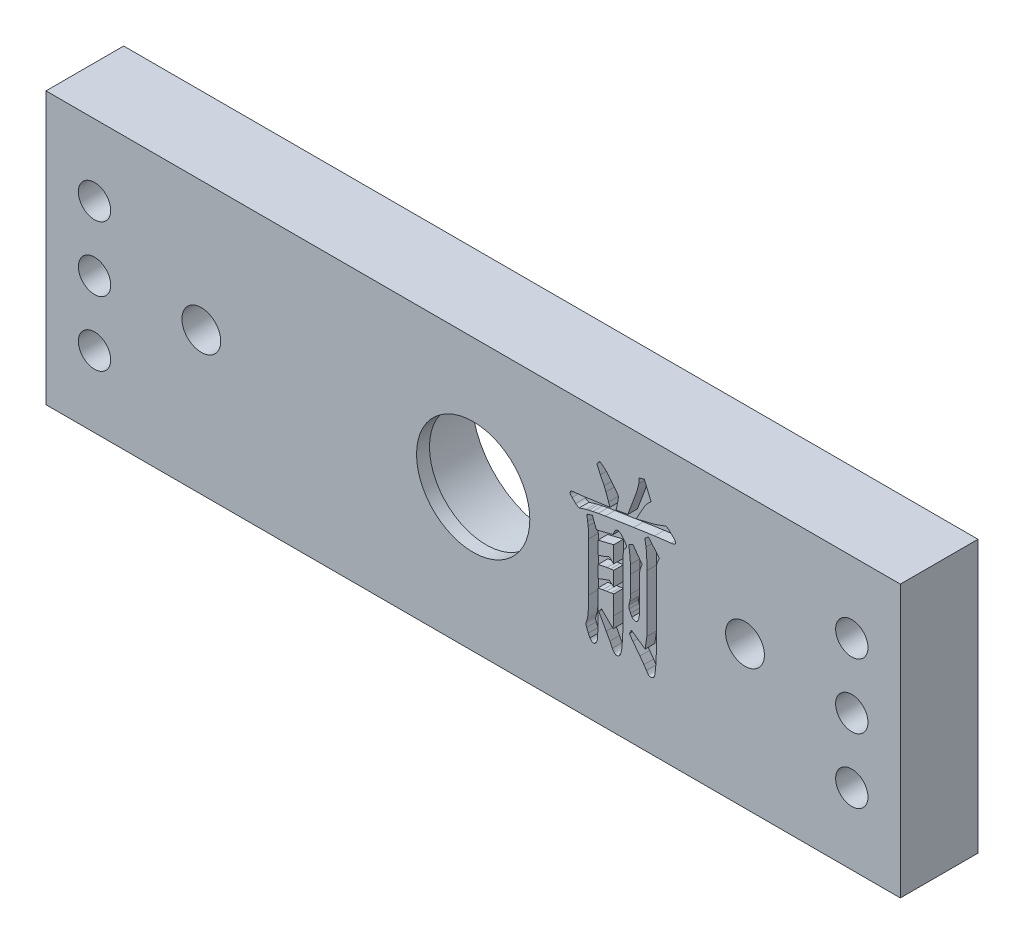
SolidWorks part; units mm, degrees
ref_plane "前视基准面" through (0, 0, 0) normal (0, 0, 1) x (1, 0, 0)
ref_plane "上视基准面" through (0, 0, 0) normal (0, 1, 0) x (1, 0, 0)
ref_plane "右视基准面" through (0, 0, 0) normal (1, 0, 0) x (0, 0, -1)
sketch "草图1" plane through (0, 0, 0) normal (0, 0, 1) x (1, 0, 0)
  line L1 (-66, 20) -> (66, 20)
  line L2 (-66, 20) -> (-66, -22)
  line L3 (-66, -22) -> (66, -22)
  line L4 (66, 20) -> (66, -22)
  dimension "D1" = 42
  dimension "D2" = 132
  dimension "D3" = 66
  dimension "D4" = 20
extrude "凸台-拉伸1" add sketch "草图1" along normal blind 12
sketch "草图2" plane through (0, 0, 0) normal (0, 0, -1) x (-1, 0, 0)
  circle A0 centre (0, 0) radius 12.25
  dimension "D1" = 24.5
extrude "切除-拉伸1" cut sketch "草图2" against normal blind 10
sketch "草图3" plane through (0, 0, 0) normal (0, 0, -1) x (-1, 0, 0)
  circle A0 centre (-42, 0) radius 4.1
  circle A1 centre (42, 0) radius 4.1
  dimension "D1" = 8.2
  dimension "D2" = 8.2
  dimension "D3" = 42
  dimension "D4" = 42
extrude "切除-拉伸2" cut sketch "草图3" against normal blind 4
sketch "草图4" plane through (0, 0, 10) normal (0, 0, -1) x (-1, 0, 0)
  circle A0 centre (0, 0) radius 8.75
  dimension "D1" = 17.5
extrude "切除-拉伸3" cut sketch "草图4" against normal blind 6
sketch "草图5" plane through (0, 0, 4) normal (0, 0, -1) x (-1, 0, 0)
  circle A0 centre (-42, 0) radius 3
  circle A1 centre (42, 0) radius 3
  dimension "D1" = 6
  dimension "D2" = 6
extrude "切除-拉伸4" cut sketch "草图5" against normal blind 8
sketch "草图6" plane through (0, 0, 12) normal (0, 0, 1) x (1, 0, 0)
  line L0 (25.1918, 8.3272) -> (27.1146, 8.7921)
  line L1 (27.1146, 8.7921) -> (27.6978, 8.9182)
  line L2 (27.6978, 8.9182) -> (28.2849, 9.0955)
  line L3 (28.2849, 9.0955) -> (28.8996, 9.328)
  line L4 (28.8996, 9.328) -> (29.1478, 9.4265)
  line L5 (29.1478, 9.4265) -> (29.8177, 9.659)
  line L6 (29.8177, 9.659) -> (30.2984, 9.328)
  line L7 (30.2984, 9.328) -> (30.8303, 8.8276)
  line L8 (30.59, 7.7716) -> (28.0209, 7.4603)
  line L9 (28.0209, 7.4603) -> (24.8095, 6.9875)
  line L10 (24.8095, 6.9875) -> (20.4003, 6.3097)
  line L11 (20.4003, 6.3097) -> (19.3207, 6.1285)
  line L12 (19.3207, 6.1285) -> (18.4696, 5.9472)
  line L13 (18.4696, 5.9472) -> (17.8707, 5.8172)
  line L14 (17.8707, 5.8172) -> (17.4924, 5.7344)
  line L15 (17.4924, 5.7344) -> (16.4009, 5.4035)
  line L16 (15.8414, 5.7226) -> (15.2976, 6.2427)
  line L17 (15.1006, 7.0544) -> (17.1299, 7.279)
  line L18 (17.1299, 7.279) -> (20.9677, 7.8267)
  line L19 (20.9677, 7.8267) -> (21.1336, 7.8433)
  line L20 (22.0543, 7.9656) -> (22.3508, 8.0119)
  line L21 (22.3508, 8.0119) -> (23.8757, 8.2484)
  line L22 (25.5858, 13.225) -> (25.6449, 14.0249)
  line L23 (25.6449, 14.0249) -> (26.4408, 14.2534)
  line L24 (26.4408, 14.2534) -> (27.489, 11.7513)
  line L25 (19.0409, 3.7879) -> (21.6061, 4.4302)
  line L26 (21.6061, 4.4302) -> (21.8661, 5.037)
  line L27 (22.9103, 5.0725) -> (23.4186, 4.4381)
  line L28 (23.6353, 3.7091) -> (23.2255, 3.1851)
  line L29 (23.1783, 2.2827) -> (23.1783, -5.9171)
  line L30 (21.5076, -10.8346) -> (21.1175, -10.0544)
  line L31 (21.1175, -10.0544) -> (20.5461, -9.0181)
  line L32 (20.5461, -9.0181) -> (19.3956, -6.9376)
  line L33 (19.3956, -6.9376) -> (19.829, -6.3938)
  line L34 (19.829, -6.3938) -> (21.6218, -8.1591)
  line L35 (21.7203, -6.3584) -> (21.7203, -3.4525)
  line L36 (21.7203, 3.126) -> (19.2892, 2.5388)
  line L37 (19.2892, 2.5388) -> (19.2892, 0.5214)
  line L38 (21.0032, 1.1755) -> (21.7203, 0.5627)
  line L39 (21.212, -0.373) -> (20.684, -0.4361)
  line L40 (20.684, -0.4361) -> (19.2892, -0.7316)
  line L41 (19.2892, -0.7316) -> (19.2892, -2.6111)
  line L42 (21.0465, -1.9571) -> (21.7203, -2.5391)
  line L43 (21.3066, -3.5332) -> (20.6131, -3.6356)
  line L44 (20.6131, -3.6356) -> (20.0221, -3.742)
  line L45 (20.0221, -3.742) -> (19.2892, -3.872)
  line L46 (19.2892, -3.872) -> (19.2852, -8.1394)
  line L47 (19.2852, -8.1394) -> (19.2576, -9.6604)
  line L48 (19.2576, -9.6604) -> (19.2025, -10.6809)
  line L49 (18.0322, -11.1892) -> (17.7918, -10.6809)
  line L50 (17.7918, -10.6809) -> (17.5357, -10.015)
  line L51 (17.8273, -5.5782) -> (17.8273, 1.9675)
  line L52 (17.7761, 3.654) -> (17.6736, 4.2489)
  line L53 (17.6736, 4.2489) -> (17.5673, 5.1473)
  line L54 (17.5673, 5.1473) -> (18.4105, 5.431)
  line L55 (18.4105, 5.431) -> (19.0409, 3.7879)
  line L56 (19.5847, 13.2092) -> (20.4437, 12.5197)
  line L57 (20.4437, 12.5197) -> (20.9441, 11.9404)
  line L58 (20.9441, 11.9404) -> (21.4169, 11.3651)
  line L59 (21.4169, 11.3651) -> (22.0001, 10.6559)
  line L60 (22.3863, 9.4108) -> (22.1735, 8.3626)
  line L61 (21.1293, 7.8543) -> (20.9205, 8.4611)
  line L62 (20.9205, 8.4611) -> (20.5028, 9.5999)
  line L63 (20.5028, 9.5999) -> (20.227, 10.2855)
  line L64 (20.227, 10.2855) -> (19.6556, 11.4597)
  line L65 (19.6556, 11.4597) -> (19.1079, 12.6852)
  line L66 (19.1079, 12.6852) -> (19.5847, 13.2092)
  line L67 (24.0412, 4.3199) -> (24.7032, 4.6233)
  line L68 (24.7032, 4.6233) -> (26.1296, 2.6413)
  line L69 (25.7119, 1.1322) -> (25.7119, -3.6435)
  line L70 (24.5337, -5.1448) -> (24.3249, -4.7507)
  line L71 (24.3249, -4.7507) -> (24.1082, -4.27)
  line L72 (24.0451, -3.7814) -> (24.183, -3.2771)
  line L73 (24.3288, -2.162) -> (24.3012, 0.4741)
  line L74 (24.3012, 0.4741) -> (24.3012, 1.7981)
  line L75 (24.4628, -6.9416) -> (26.5709, -8.4152)
  line L76 (26.8349, -6.5948) -> (26.8349, 2.2276)
  line L77 (26.7048, 5.3128) -> (26.5236, 6.3846)
  line L78 (26.5236, 6.3846) -> (27.0831, 6.8653)
  line L79 (27.0831, 6.8653) -> (28.7656, 4.8439)
  line L80 (28.2967, 2.3852) -> (28.2967, -8.1867)
  line L81 (28.21, -9.885) -> (28.1312, -10.6691)
  line L82 (26.7679, -11.1656) -> (26.3778, -10.5785)
  line L83 (26.3778, -10.5785) -> (25.771, -9.7234)
  line L84 (25.771, -9.7234) -> (24.6913, -8.3404)
  line L85 (24.6913, -8.3404) -> (24.1476, -7.5405)
  line L86 (24.1476, -7.5405) -> (24.4628, -6.9416)
  line L87 (21.7203, 0.5627) -> (21.7203, 3.126)
  line L88 (21.7203, -2.5391) -> (21.7203, -0.2932)
  line L89 (21.7203, -6.3584) -> (21.6218, -8.1591)
  line L90 (26.8349, -6.5948) -> (26.5709, -8.4152)
  spline S0 degree 3 poles (30.8303, 8.8276) (30.9744, 8.6945) (31.1391, 8.499) (31.2842, 8.2301) (31.2861, 8.0724) (31.1985, 7.9521) (30.9693, 7.8226) (30.7475, 7.7999) (30.59, 7.7716) knots 0 0 0 0 0.347386 0.457637 0.53741 0.613513 0.710465 1 1 1 1
  spline S1 degree 2 poles (16.4009, 5.4035) (16.0728, 5.4755) (15.8414, 5.7226) knots 0 0 0 1 1 1
  spline S2 degree 3 poles (15.2976, 6.2427) (15.214, 6.3213) (15.0998, 6.4262) (15.005, 6.5827) (14.956, 6.7793) (15.0657, 6.9388) (15.1006, 7.0544) knots 0 0 0 0 0.367731 0.487674 0.578039 1 1 1 1
  spline S3 degree 3 poles (23.8757, 8.2484) (24.0035, 8.5899) (24.2006, 9.0762) (24.4317, 9.705) (24.5935, 10.1078) (24.7245, 10.4742) (24.8484, 10.7943) (24.9507, 11.076) (25.0622, 11.386) (25.1843, 11.7218) (25.3016, 12.0834) (25.3954, 12.3954) (25.456, 12.6599) (25.5036, 12.8729) (25.5426, 13.0561) (25.5699, 13.1676) (25.5858, 13.225) knots 0 0 0 0 0.207633 0.298753 0.381388 0.45474 0.520301 0.576848 0.625344 0.707897 0.780266 0.841801 0.893317 0.934687 0.966079 1 1 1 1
  spline S4 degree 3 poles (27.489, 11.7513) (27.3166, 11.6039) (27.0782, 11.39) (26.8064, 11.0984) (26.6694, 10.9273) (26.563, 10.7652) (26.4556, 10.589) (26.3203, 10.3536) (26.1489, 10.0626) (25.9535, 9.7103) (25.627, 9.1276) (25.372, 8.6587) (25.1918, 8.3272) knots 0 0 0 0 0.163792 0.230902 0.287626 0.321818 0.370773 0.436645 0.517807 0.614614 0.727539 1 1 1 1
  spline S5 degree 3 poles (21.8661, 5.037) (21.9316, 5.1603) (22.0667, 5.3139) (22.311, 5.3773) (22.5853, 5.3094) (22.7721, 5.1729) (22.9103, 5.0725) knots 0 0 0 0 0.341138 0.451231 0.589089 1 1 1 1
  spline S6 degree 3 poles (23.4186, 4.4381) (23.4911, 4.3284) (23.591, 4.1866) (23.6748, 4.0045) (23.6983, 3.867) (23.6572, 3.7728) (23.6353, 3.7091) knots 0 0 0 0 0.489758 0.643143 0.741981 1 1 1 1
  spline S7 degree 3 poles (23.2255, 3.1851) (23.2035, 3.1054) (23.1864, 2.9905) (23.1819, 2.8278) (23.1741, 2.6085) (23.1812, 2.4219) (23.1783, 2.2827) knots 0 0 0 0 0.273514 0.382334 0.538971 1 1 1 1
  spline S8 degree 3 poles (23.1783, -5.9171) (23.1805, -6.0393) (23.1743, -6.2375) (23.1709, -6.5239) (23.1627, -6.7853) (23.1499, -7.0781) (23.1381, -7.4025) (23.1275, -7.7586) (23.1061, -8.2551) (23.0808, -8.8412) (23.0384, -9.4667) (22.99, -9.973) (22.9308, -10.3688) (22.8661, -10.6751) (22.8008, -10.9145) (22.7302, -11.0985) (22.6203, -11.2678) (22.4267, -11.3971) (22.2013, -11.4735) (21.986, -11.4379) (21.7293, -11.2415) (21.6053, -11.0036) (21.5076, -10.8346) knots 0 0 0 0 0.053419 0.086736 0.125234 0.16777 0.214897 0.267191 0.323523 0.432196 0.523735 0.597629 0.65457 0.698614 0.734431 0.763016 0.784521 0.821511 0.862616 0.885373 0.913888 1 1 1 1
  spline S10 degree 3 poles (19.2892, 0.5214) (19.6067, 0.617) (20.1939, 0.7958) (20.7529, 1.0491) (21.0032, 1.1755) knots 0 0 0 0 0.541942 1 1 1 1
  spline S11 degree 3 poles (21.7203, -0.2932) (21.553, -0.3312) (21.3825, -0.3562) (21.212, -0.373) knots 0.675613 0.675613 0.675613 0.675613 1 1 1 1
  spline S12 degree 3 poles (19.2892, -2.6111) (19.5523, -2.5165) (20.1398, -2.303) (20.7236, -2.0796) (21.0465, -1.9571) knots 0 0 0 0 0.447378 1 1 1 1
  spline S13 degree 3 poles (21.7203, -3.4525) (21.5845, -3.4885) (21.4454, -3.5118) (21.3066, -3.5332) knots 0.741321 0.741321 0.741321 0.741321 1 1 1 1
  spline S14 degree 3 poles (19.2025, -10.6809) (19.1886, -10.8452) (19.1538, -11.0959) (18.976, -11.363) (18.8226, -11.5168) (18.6299, -11.612) (18.3019, -11.5526) (18.1418, -11.3256) (18.0322, -11.1892) knots 0 0 0 0 0.265053 0.383706 0.501207 0.607272 0.707999 1 1 1 1
  spline S15 degree 3 poles (17.5357, -10.015) (17.4773, -9.8851) (17.396, -9.6923) (17.4488, -9.4533) (17.487, -9.2926) (17.5511, -9.0823) (17.6299, -8.8714) (17.6845, -8.644) (17.7216, -8.4016) (17.7573, -8.0928) (17.7829, -7.7181) (17.8013, -7.2766) (17.8249, -6.5569) (17.824, -5.9827) (17.8273, -5.5782) knots 0 0 0 0 0.100293 0.125218 0.1622 0.210716 0.271682 0.312278 0.366447 0.435254 0.519605 0.616976 0.730077 1 1 1 1
  spline S16 degree 3 poles (17.8273, 1.9675) (17.8245, 2.2893) (17.8242, 2.852) (17.7974, 3.4141) (17.7761, 3.654) knots 0 0 0 0 0.572057 1 1 1 1
  spline S17 degree 3 poles (22.0001, 10.6559) (22.1102, 10.5083) (22.2565, 10.3122) (22.3955, 10.0631) (22.4717, 9.7977) (22.3911, 9.577) (22.3863, 9.4108) knots 0 0 0 0 0.402738 0.535126 0.621583 1 1 1 1
  spline S18 degree 3 poles (22.1735, 8.3626) (22.1491, 8.2261) (22.1134, 8.0907) (22.0543, 7.9656) knots 0 0 0 0 0.260339 0.260339 0.260339 0.260339
  spline S19 degree 3 poles (26.1296, 2.6413) (25.9893, 2.4287) (25.7744, 1.9381) (25.7133, 1.4066) (25.7119, 1.1322) knots 0 0 0 0 0.480509 1 1 1 1
  spline S20 degree 3 poles (25.7119, -3.6435) (25.7149, -3.9568) (25.6903, -4.395) (25.5685, -4.9189) (25.4692, -5.1684) (25.3634, -5.3179) (25.2774, -5.3957) (25.176, -5.4398) (25.0643, -5.4396) (24.9435, -5.4151) (24.7524, -5.332) (24.6247, -5.2208) (24.5337, -5.1448) knots 0 0 0 0 0.351023 0.487127 0.600936 0.648243 0.690945 0.72914 0.768831 0.813774 0.866434 1 1 1 1
  spline S21 degree 2 poles (24.1082, -4.27) (24.0242, -4.0322) (24.0451, -3.7814) knots 0 0 0 1 1 1
  spline S22 degree 3 poles (24.183, -3.2771) (24.2346, -3.136) (24.2915, -2.7631) (24.3344, -2.3896) (24.3288, -2.162) knots 0 0 0 0 0.397178 1 1 1 1
  spline S23 degree 3 poles (24.3012, 1.7981) (24.2834, 2.0607) (24.2661, 2.4146) (24.2238, 2.8937) (24.1644, 3.4729) (24.0895, 3.9587) (24.0412, 4.3199) knots 0 0 0 0 0.311368 0.418968 0.568917 1 1 1 1
  spline S25 degree 3 poles (26.8349, 2.2276) (26.8252, 2.6714) (26.8405, 3.2773) (26.8128, 4.0034) (26.7983, 4.3818) (26.7785, 4.6801) (26.7481, 4.9823) (26.725, 5.1886) (26.7048, 5.3128) knots 0 0 0 0 0.430919 0.587813 0.705214 0.798498 0.877911 1 1 1 1
  spline S26 degree 3 poles (28.7656, 4.8439) (28.6653, 4.6267) (28.5159, 4.3304) (28.3951, 3.9506) (28.3364, 3.7262) (28.323, 3.4858) (28.2956, 3.0387) (28.302, 2.662) (28.2967, 2.3852) knots 0 0 0 0 0.283364 0.389307 0.470566 0.556221 0.672708 1 1 1 1
  spline S27 degree 3 poles (28.2967, -8.1867) (28.2987, -8.4879) (28.2688, -9.0542) (28.2328, -9.62) (28.21, -9.885) knots 0 0 0 0 0.530905 1 1 1 1
  spline S28 degree 3 poles (28.1312, -10.6691) (28.0976, -10.9143) (28.0676, -11.2453) (27.8673, -11.598) (27.6818, -11.6953) (27.5159, -11.7134) (27.3747, -11.7227) (27.2626, -11.7209) (27.164, -11.7037) (27.0806, -11.6324) (26.9333, -11.4643) (26.8478, -11.2859) (26.7679, -11.1656) knots 0 0 0 0 0.315764 0.418272 0.498355 0.571215 0.629844 0.678372 0.714475 0.753944 0.814359 1 1 1 1
  spline S29 degree 2 poles (21.1336, 7.8433) (21.1313, 7.8488) (21.1293, 7.8543) knots 0.992819 0.992819 0.992819 1 1 1
extrude "切除-拉伸6" cut sketch "草图6" against normal blind 1.5
sketch "草图7" plane through (0, 0, 0) normal (0, 0, -1) x (-1, 0, 0)
  line L0 (0, 0) -> (0, -29.2112)
  line L1 (-66, 20) -> (66, 20) construction
  line L2 (66, 20) -> (66, -22) construction
  circle A0 centre (58.5, 9) radius 2.5
  circle A1 centre (58.5, -1) radius 2.5
  circle A2 centre (58.5, -11) radius 2.5
  circle A3 centre (-58.5, -11) radius 2.5
  circle A4 centre (-58.5, -1) radius 2.5
  circle A5 centre (-58.5, 9) radius 2.5
  dimension "D1" = 5
  dimension "D2" = 5
  dimension "D3" = 5
  dimension "D4" = 11
  dimension "D5" = 10
  dimension "D6" = 10
  dimension "D7" = 7.5
extrude "切除-拉伸7" cut sketch "草图7" against normal blind 12 contours A5 | A4 | A3 | A0 | A1 | A2
